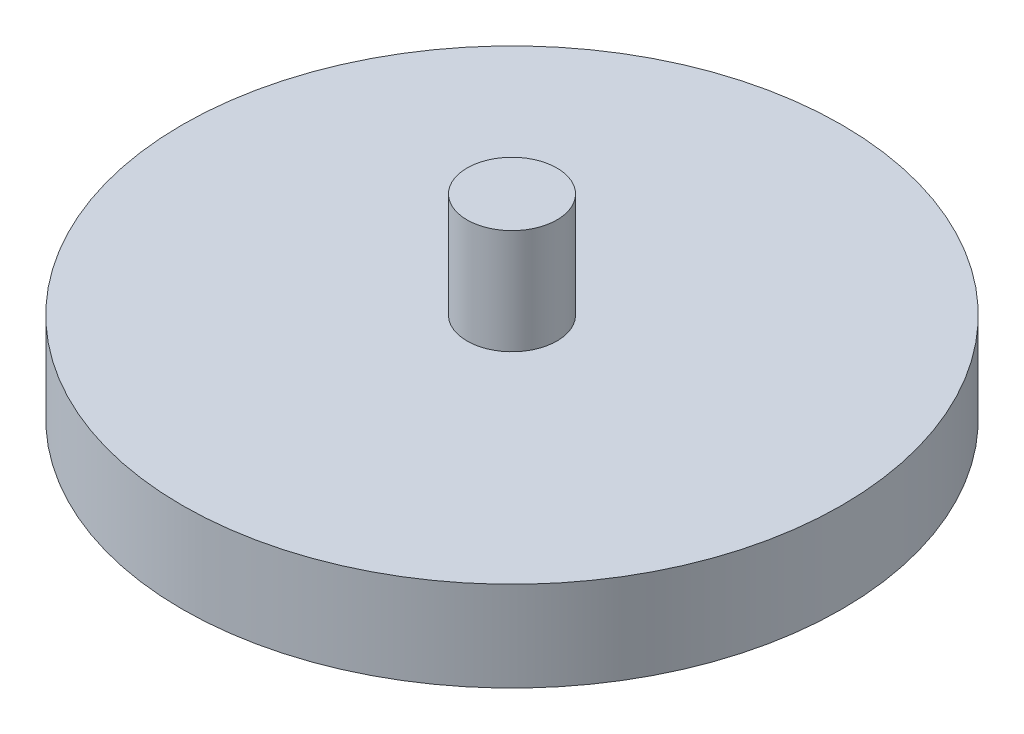
SolidWorks part; units mm, degrees
ref_plane "Płaszczyzna przednia" through (0, 0, 0) normal (0, 0, 1) x (1, 0, 0)
ref_plane "Płaszczyzna górna" through (0, 0, 0) normal (0, 1, 0) x (1, 0, 0)
ref_plane "Płaszczyzna prawa" through (0, 0, 0) normal (1, 0, 0) x (0, 0, -1)
sketch "Szkic2" plane through (0, 0, 0) normal (0, 1, 0) x (1, 0, 0)
  circle A0 centre (0, 0) radius 220
  dimension "D1" = 440
extrude "Dodanie-wyciągnięcie1" add sketch "Szkic2" along normal blind 60
sketch "Szkic3" plane through (0, 60, 0) normal (0, 1, 0) x (1, 0, 0)
  circle A0 centre (0, 0) radius 30
  dimension "D1" = 60
extrude "Dodanie-wyciągnięcie2" add sketch "Szkic3" along normal blind 70
sketch "Szkic4" plane through (0, 0, 0) normal (0, -1, 0) x (1, 0, 0)
  circle A0 centre (0, 0) radius 30
  dimension "D1" = 60
extrude "Dodanie-wyciągnięcie3" add sketch "Szkic4" along normal blind 70
